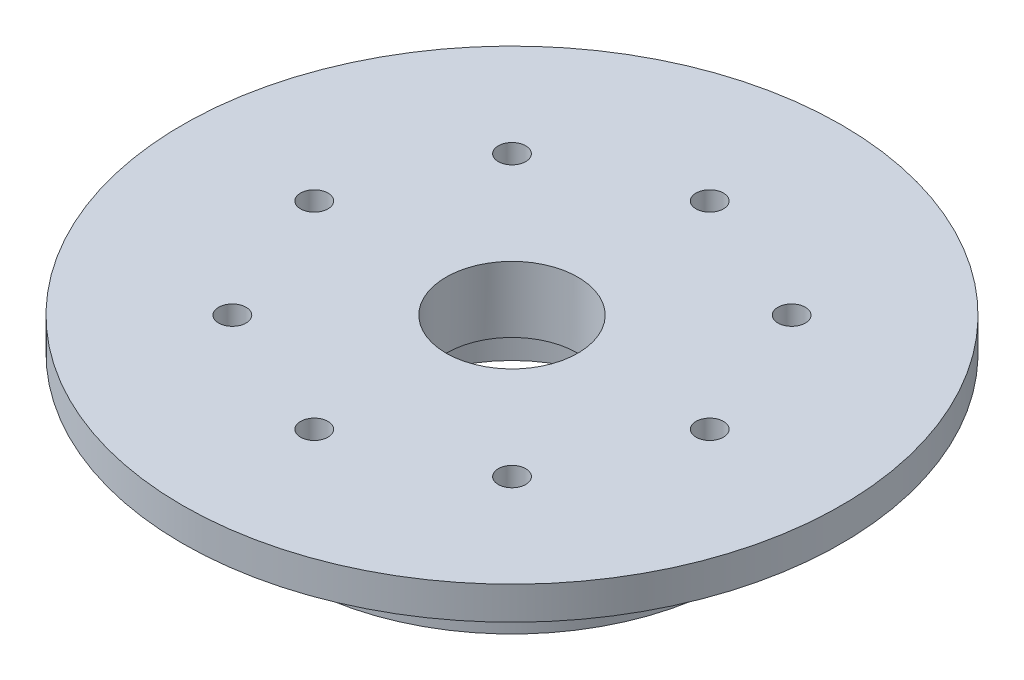
SolidWorks part; units mm, degrees
material "Custom Plastic-PLA"
ref_plane "Front Plane" through (0, 0, 0) normal (0, 0, 1) x (1, 0, 0)
ref_plane "Top Plane" through (0, 0, 0) normal (0, 1, 0) x (1, 0, 0)
ref_plane "Right Plane" through (0, 0, 0) normal (1, 0, 0) x (0, 0, -1)
sketch "Sketch1" plane through (0, 0, 0) normal (0, 1, 0) x (1, 0, 0)
  circle A0 centre (0, 0) radius 30
extrude "Boss-Extrude1" add sketch "Sketch1" against normal blind 3
sketch "Sketch2" plane through (0, -3, 0) normal (0, -1, 0) x (1, 0, 0)
  circle A0 centre (0, 0) radius 23
extrude "Boss-Extrude2" add sketch "Sketch2" along normal blind 1
sketch "Sketch3" plane through (0, -4, 0) normal (0, -1, 0) x (1, 0, 0)
  circle A0 centre (0, 0) radius 20
extrude "Boss-Extrude3" add sketch "Sketch3" along normal blind 7
sketch "Sketch12" plane through (0, -11, 0) normal (0, -1, 0) x (1, 0, 0)
  circle A0 centre (0, 0) radius 10.5
extrude "Cut-Extrude1" cut sketch "Sketch12" against normal blind 5
sketch "Sketch16" plane through (0, 0, 0) normal (0, 1, 0) x (1, 0, 0)
  circle A0 centre (0, 0) radius 6
extrude "Cut-Extrude2" cut sketch "Sketch16" against normal through all
sketch "Sketch22" plane through (0, 0, 0) normal (0, 1, 0) x (1, 0, 0)
  circle A0 centre (0, 0) radius 18 construction
  point P11 (0, 18)
  point P20 (12.7279, 12.7279)
  point P21 (18, 0)
  point P22 (12.7279, -12.7279)
  point P23 (0, -18)
  point P24 (-12.7279, -12.7279)
  point P25 (-18, 0)
  point P26 (-12.7279, 12.7279)
  dimension "D1" = 8
hole_wizard "M3 Tapped Hole1" positions "Sketch22" profile "Sketch24" tap size "M3" standard "ISO"
sketch "Sketch24" plane through (-12.7279, 0, -12.7279) normal (1, 0, 0) x (0, 0, 1)
  line L0 (0, 0) -> (0, 30)
  line L1 (0, 30) -> (1.25, 29.2489)
  line L2 (1.25, 29.2489) -> (1.25, 0)
  line L5 (1.25, 0) -> (0, 0)
  line L10 (0, 30) -> (-1.25, 29.2489) construction
  line L11 (0, -6.35) -> (0, 107.95) construction
  dimension "Tap Drill Dia." = 2.5
  dimension "Tap Drill Depth" = 30
  dimension "Drill Angle" = 118
